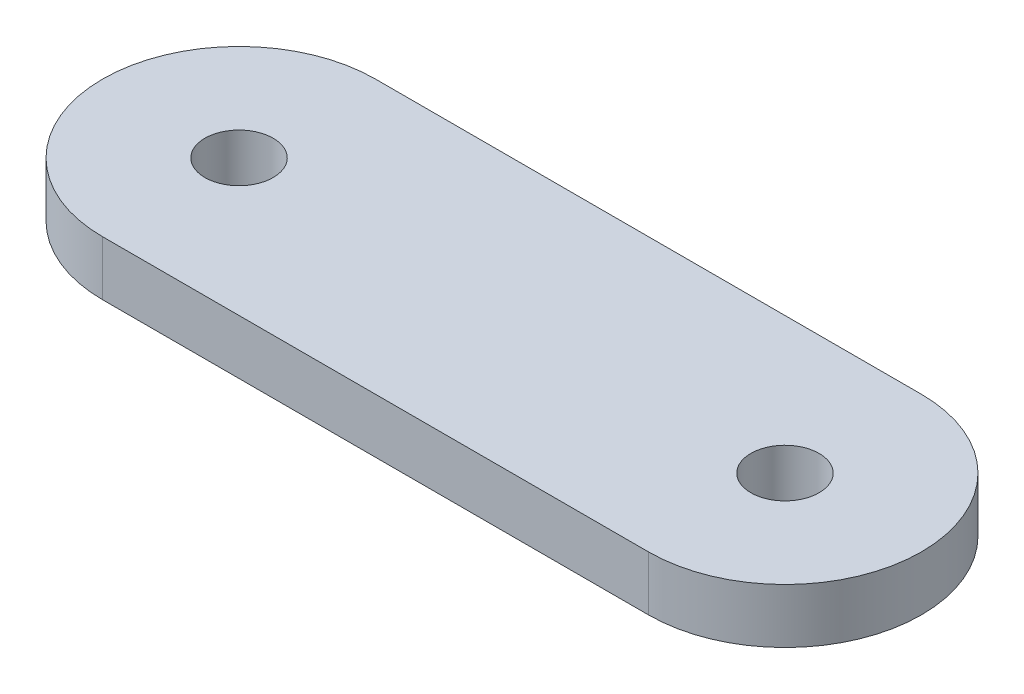
SolidWorks part; units mm, degrees
ref_plane "Front Plane" through (0, 0, 0) normal (0, 0, 1) x (1, 0, 0)
ref_plane "Top Plane" through (0, 0, 0) normal (0, 1, 0) x (1, 0, 0)
ref_plane "Right Plane" through (0, 0, 0) normal (1, 0, 0) x (0, 0, -1)
sketch "Sketch1" plane through (0, 0, 0) normal (0, 1, 0) x (1, 0, 0)
  line L0 (0, 0) -> (20, 0) construction
  line L1 (0, 5) -> (20, 5)
  line L2 (0, -5) -> (20, -5)
  arc A0 (0, 5) -> (0, -5) centre (0, 0) ccw
  arc A1 (20, -5) -> (20, 5) centre (20, 0) ccw
  circle A2 centre (0, 0) radius 1.25
  circle A3 centre (20, 0) radius 1.25
  point P3 (10, 0)
  dimension "D3" = 2.5
  dimension "D1" = 10
  dimension "D2" = 20
extrude "Boss-Extrude1" add sketch "Sketch1" along normal blind 2
